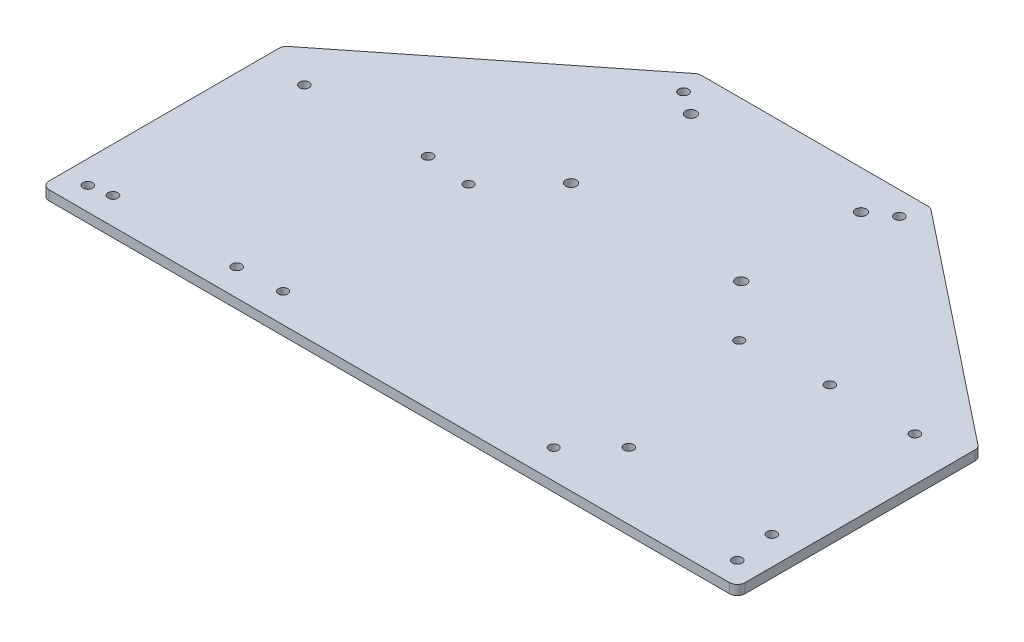
SolidWorks part; units mm, degrees
material "Corrugated Paper"
ref_plane "Front Plane" through (0, 0, 0) normal (0, 0, 1) x (1, 0, 0)
ref_plane "Top Plane" through (0, 0, 0) normal (0, 1, 0) x (1, 0, 0)
ref_plane "Right Plane" through (0, 0, 0) normal (1, 0, 0) x (0, 0, -1)
sketch "Sketch1" plane through (0, 0, 0) normal (0, 1, 0) x (1, 0, 0)
  line L0 (86.36, 0) -> (86.36, 139.7) construction
  line L1 (0, 0) -> (228.6, 0)
  line L2 (0, 0) -> (0, 139.7)
  line L3 (0, 139.7) -> (228.6, 139.7)
  line L4 (228.6, 0) -> (228.6, 139.7)
  line L5 (142.24, 139.7) -> (142.24, 0) construction
  line L6 (0, 87.63) -> (228.6, 87.63) construction
  line L7 (0, 127) -> (228.6, 127) construction
  line L8 (114.3, 139.7) -> (114.3, 0) construction
  line L9 (86.36, 20.2473) -> (142.24, 20.2473) construction
  line L10 (0, 69.85) -> (228.6, 69.85) construction
  circle A0 centre (86.36, 127) radius 1.778
  circle A1 centre (142.24, 127) radius 1.778
  circle A2 centre (86.36, 87.63) radius 1.778
  circle A3 centre (142.24, 87.63) radius 1.778
  point P25 (114.3, 20.2473)
  dimension "D7" = 3.556
  dimension "D8" = 3.556
  dimension "D9" = 3.556
  dimension "D10" = 3.556
  dimension "D1" = 228.6
  dimension "D2" = 139.7
  dimension "D3" = 55.88
  dimension "D4" = 39.37
  dimension "D5" = 12.7
extrude "Boss-Extrude1" add sketch "Sketch1" along normal blind 3.175
sketch "Sketch2" plane through (0, 3.175, 0) normal (0, 1, 0) x (1, 0, 0)
  line L0 (114.3, 139.7) -> (114.3, 0) construction
  line L1 (228.6, 139.7) -> (0, 139.7) construction
  line L2 (0, 0) -> (228.6, 0) construction
  line L3 (0, 69.85) -> (228.6, 69.85) construction
  line L4 (0, 139.7) -> (0, 0) construction
  line L5 (228.6, 0) -> (228.6, 139.7) construction
sketch "Sketch3" plane through (0, 3.175, 0) normal (0, 1, 0) x (1, 0, 0)
  line L0 (114.3, 139.7) -> (114.3, 0) construction
  line L1 (69.85, 9.525) -> (158.75, 9.525)
  line L2 (69.85, 9.525) -> (69.85, 70.485)
  line L3 (69.85, 70.485) -> (158.75, 70.485)
  line L4 (158.75, 9.525) -> (158.75, 70.485)
  line L5 (0, 0) -> (228.6, 0) construction
  circle A0 centre (69.85, 70.485) radius 1.524
  circle A1 centre (158.75, 70.485) radius 1.524
  circle A2 centre (158.75, 9.525) radius 1.524
  circle A3 centre (69.85, 9.525) radius 1.524
  point P8 (114.3, 9.525)
  dimension "D3" = 3.048
  dimension "D4" = 3.048
  dimension "D5" = 3.048
  dimension "D6" = 3.048
  dimension "D1" = 88.9
  dimension "D2" = 60.96
  dimension "D7" = 9.525
extrude "Cut-Extrude1" cut sketch "Sketch3" against normal through all contours A0 | A1 | A2 | A3
sketch "Sketch4" plane through (0, 3.175, 0) normal (0, 1, 0) x (1, 0, 0)
  line L0 (0, 0) -> (228.6, 0) construction
  line L1 (171.0182, 21.9481) -> (219.2782, 21.9481)
  line L2 (171.0182, 21.9481) -> (171.0182, 72.7481)
  line L3 (171.0182, 72.7481) -> (219.2782, 72.7481)
  line L4 (219.2782, 21.9481) -> (219.2782, 72.7481)
  line L5 (228.6, 0) -> (228.6, 139.7) construction
  circle A0 centre (171.0182, 21.9481) radius 1.5875
  circle A2 centre (186.2582, 72.7481) radius 1.5875
  circle A3 centre (214.1982, 72.7481) radius 1.5875
  circle A4 centre (219.2782, 20.6781) radius 1.5875
  dimension "D5" = 3.175
  dimension "D6" = 3.175
  dimension "D7" = 3.175
  dimension "D8" = 3.175
  dimension "D1" = 48.26
  dimension "D2" = 50.8
  dimension "D3" = 5.08
  dimension "D4" = 27.94
  dimension "D9" = 21.9481
  dimension "D10" = 9.3218
  dimension "D11" = 1.27
extrude "Cut-Extrude2" cut sketch "Sketch4" against normal through all
sketch "Sketch5" plane through (0, 3.175, 0) normal (0, 1, 0) x (1, 0, 0)
  line L0 (34.925, 71.755) -> (34.925, 8.89) construction
  line L1 (14.605, 8.89) -> (55.245, 8.89)
  line L2 (14.605, 8.89) -> (14.605, 71.755)
  line L3 (14.605, 71.755) -> (55.245, 71.755)
  line L4 (55.245, 8.89) -> (55.245, 71.755)
  line L5 (69.85, 9.525) -> (0, 9.525) construction
  line L6 (0, 139.7) -> (0, 0) construction
  line L7 (0, 0) -> (228.6, 0) construction
  circle A0 centre (14.605, 71.755) radius 1.5875
  circle A1 centre (55.245, 71.755) radius 1.5875
  circle A2 centre (55.245, 8.89) radius 1.5875
  circle A3 centre (14.605, 8.89) radius 1.5875
  point P15 (34.925, 9.525)
  dimension "D3" = 3.175
  dimension "D4" = 3.175
  dimension "D5" = 3.175
  dimension "D6" = 3.175
  dimension "D1" = 62.865
  dimension "D2" = 40.64
  dimension "D7" = 8.89
extrude "Cut-Extrude3" cut sketch "Sketch5" against normal through all contours A0 | A2 | A1 | A3
sketch "Sketch6" plane through (0, 3.175, 0) normal (0, 1, 0) x (1, 0, 0)
  line L0 (228.6, 79.248) -> (152.4, 139.7)
  line L1 (228.6, 0) -> (228.6, 139.7) construction
  line L2 (228.6, 139.7) -> (0, 139.7) construction
  line L3 (152.4, 139.7) -> (228.6, 139.7)
  line L4 (228.6, 139.7) -> (228.6, 79.248)
  line L5 (114.3, 139.7) -> (114.3, 0) construction
  line L6 (76.2, 139.7) -> (0, 139.7)
  line L7 (0, 79.248) -> (76.2, 139.7)
  line L8 (0, 139.7) -> (0, 79.248)
  dimension "D1" = 79.248
  dimension "D2" = 76.2
extrude "Cut-Extrude4" cut sketch "Sketch6" against normal through all
fillet "Fillet1" radius 2.54 6 edges at (0, 1.5875, -79.248) (76.2, 1.5875, -139.7) (152.4, 1.5875, -139.7) (228.6, 1.5875, -79.248) (0, 1.5875, 0) (228.6, 1.5875, 0)
sketch "Sketch7" plane through (0, 3.175, 0) normal (0, 1, 0) x (1, 0, 0)
  line L0 (228.6, 2.54) -> (228.6, 78.0208) construction
  line L1 (228.6, 0) -> (220.98, 0)
  line L2 (228.6, 0) -> (228.6, 7.62)
  line L3 (228.6, 7.62) -> (220.98, 7.62)
  line L4 (220.98, 0) -> (220.98, 7.62)
  line L5 (2.54, 0) -> (226.06, 0) construction
  line L6 (151.5148, 139.7) -> (77.0852, 139.7) construction
  line L7 (153.0935, 139.1499) -> (227.6386, 80.0107) construction
  line L8 (114.3, 139.7) -> (114.3, 0) construction
  circle A0 centre (220.98, 7.62) radius 1.5875
  circle A2 centre (149.7445, 132.08) radius 1.5875
  circle A3 centre (7.62, 7.62) radius 1.5875
  circle A4 centre (78.8555, 132.08) radius 1.5875
  dimension "D1" = 3.175
  dimension "D6" = 3.175
  dimension "D2" = 7.62
  dimension "D3" = 7.62
  dimension "D4" = 7.62
  dimension "D5" = 7.62
extrude "Cut-Extrude5" cut sketch "Sketch7" against normal through all contours A4 | A2 | A0 | A3
